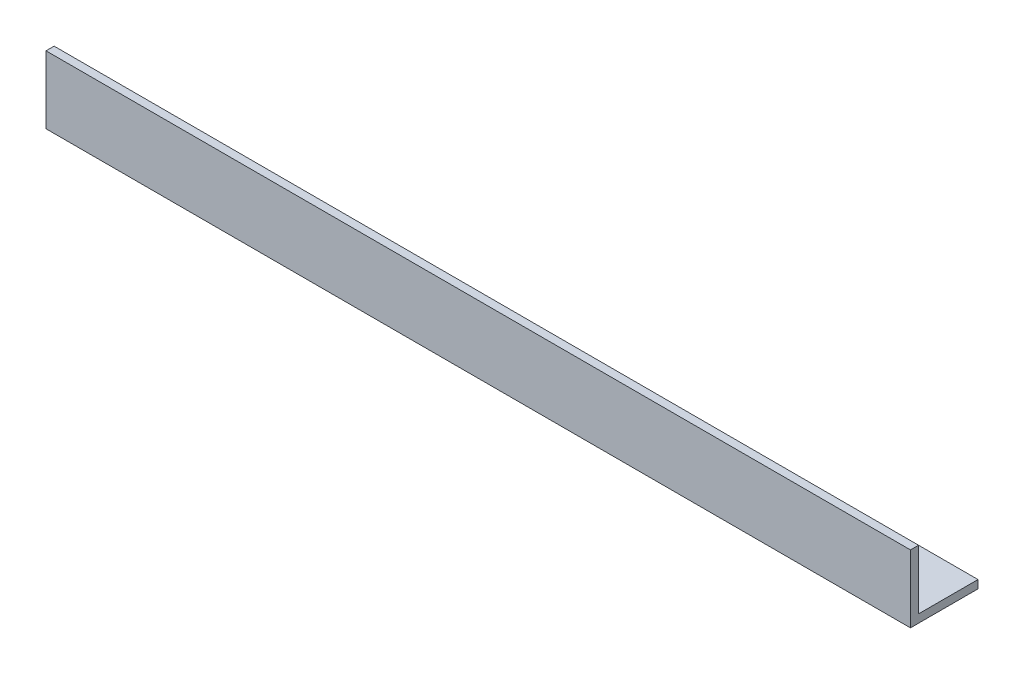
SolidWorks part; units mm, degrees
ref_plane "Спереди" through (0, 0, 0) normal (0, 0, 1) x (1, 0, 0)
ref_plane "Сверху" through (0, 0, 0) normal (0, 1, 0) x (1, 0, 0)
ref_plane "Справа" through (0, 0, 0) normal (1, 0, 0) x (0, 0, -1)
sketch "Эскиз1" plane through (0, 0, 0) normal (1, 0, 0) x (0, 0, -1)
  line L0 (0, 25) -> (0, 0)
  line L1 (0, 0) -> (25, 0)
extrude "Вытянуть-Тонкостенный1" add sketch "Эскиз1" along normal blind 320 thin thin type one direction reverse wall 3
ref_point "Точка2"
